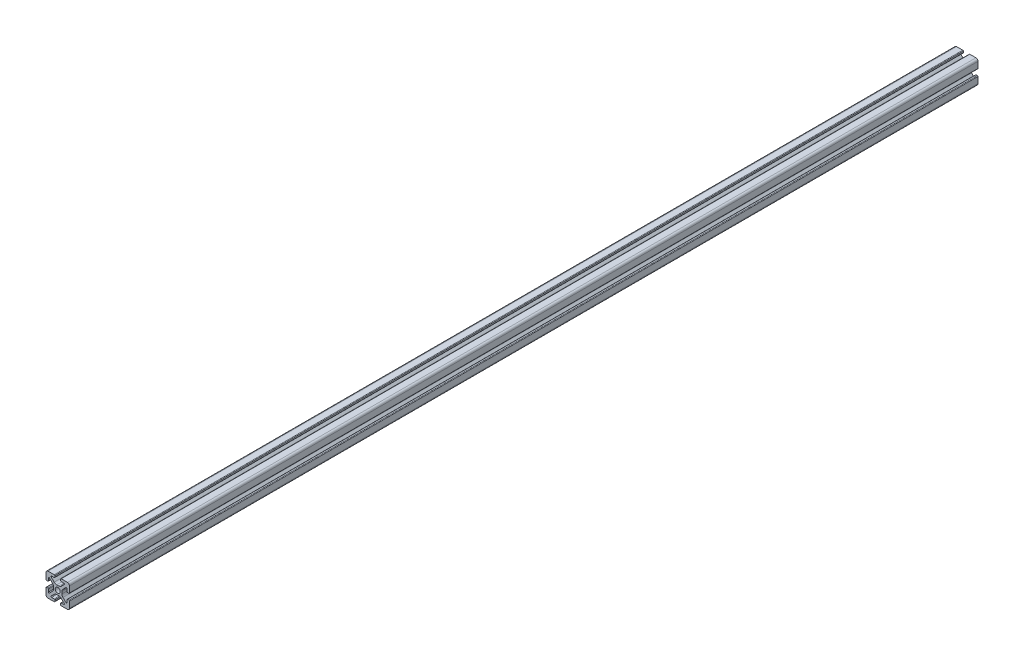
SolidWorks part; units mm, degrees
material "6061 Alloy"
ref_plane "Front Plane" through (0, 0, 0) normal (0, 0, 1) x (1, 0, 0)
ref_plane "Top Plane" through (0, 0, 0) normal (0, 1, 0) x (1, 0, 0)
ref_plane "Right Plane" through (0, 0, 0) normal (1, 0, 0) x (0, 0, -1)
sketch "Sketch2" plane through (0, 0, 0) normal (0, 0, 1) x (1, 0, 0)
  line L0 (0, 10) -> (0, -10) construction
  line L1 (-10, 0) -> (10, 0) construction
  line L2 (2.5, -10) -> (10, -10)
  line L3 (10, -10) -> (10, -2.5)
  line L4 (2.5, -10) -> (2.5, -7.9246)
  line L5 (2.5, -7.9246) -> (6.4571, -7.9246)
  line L6 (6.4571, -7.9246) -> (2.1325, -3.6)
  line L7 (0, 0) -> (10, -10) construction
  line L8 (10, -2.5) -> (7.9246, -2.5)
  line L9 (7.9246, -2.5) -> (7.9246, -6.4571)
  line L10 (7.9246, -6.4571) -> (3.6, -2.1325)
  line L11 (5.7623, -4.2948) -> (4.2948, -5.7623) construction
  circle A0 centre (0, 0) radius 2.15
  arc A1 (5.25, -7.9246) -> (5.6036, -7.0711) centre (5.25, -7.4246) ccw construction
  point P8 (0, -3.6)
  point P16 (5.0286, -5.0286)
  dimension "Center Hole Diameter" = 4.3
  dimension "D3" = 0.5
  dimension "Rail Height" = 20
  dimension "Rail Width" = 20
  dimension "T-Slot Width" = 5
  dimension "Slot Depth" = 6.4
  dimension "Slot Inner Width" = 11.5
sketch "Sketch3" plane through (0, 0, 0) normal (1, 0, 0) x (0, 0, -1)
  line L0 (-152.4, -10) -> (152.4, -10) construction
  line L1 (-127, 0) -> (127, 0) construction
  line L2 (0, 10) -> (0, -10) construction
  line L3 (0, 10) -> (0, -10) construction
  point P6 (-127, 0)
  point P8 (127, 0)
  dimension "Length" = 304.8
  dimension "D1" = 25.4
sketch "Sketch4" plane through (0, 0, 0) normal (0, 0, 1) x (1, 0, 0)
  line L0 (3, -10) -> (8.25, -10)
  line L1 (2.5, -10) -> (10, -10) construction
  line L2 (2.5, -10) -> (2.5, -7.9246) construction
  line L3 (2.5, -7.9246) -> (6.4571, -7.9246) construction
  line L4 (2.5, -8.4246) -> (2.5, -9.5)
  line L5 (3, -7.9246) -> (5.25, -7.9246)
  line L6 (0, -3.6) -> (0.8898, -3.6)
  line L7 (6.4571, -7.9246) -> (2.1325, -3.6) construction
  line L8 (3.0112, -4.4787) -> (5.6036, -7.0711)
  line L9 (10, -10) -> (10, -2.5) construction
  line L10 (7.9246, -6.4571) -> (3.6, -2.1325) construction
  line L11 (7.9246, -2.5) -> (7.9246, -6.4571) construction
  line L12 (7.9246, -5.25) -> (7.9246, -3)
  line L13 (10, -2.5) -> (7.9246, -2.5) construction
  line L14 (8.4246, -2.5) -> (9.5, -2.5)
  line L15 (10, -3) -> (10, -8.25)
  line L16 (7.0711, -5.6036) -> (4.4787, -3.0112)
  line L17 (3.6, 0) -> (3.6, -0.8898)
  line L18 (-10, 0) -> (10, 0) construction
  line L19 (0, -3.6) -> (0, -2.15)
  line L20 (0, 10) -> (0, -10) construction
  line L21 (3.6, 0) -> (2.15, 0)
  arc A0 (2.5, -9.5) -> (3, -10) centre (3, -9.5) ccw
  arc A1 (5.25, -7.9246) -> (5.6036, -7.0711) centre (5.25, -7.4246) ccw construction
  arc A2 (2.5, -8.4246) -> (3, -7.9246) centre (3, -8.4246) cw
  arc A3 (5.25, -7.9246) -> (5.6036, -7.0711) centre (5.25, -7.4246) ccw
  arc A4 (0.8898, -3.6) -> (3.0112, -4.4787) centre (0.8898, -6.6) cw
  arc A5 (8.25, -10) -> (10, -8.25) centre (8.25, -8.25) ccw
  arc A6 (7.0711, -5.6036) -> (7.9246, -5.25) centre (7.4246, -5.25) ccw
  arc A7 (7.9246, -3) -> (8.4246, -2.5) centre (8.4246, -3) cw
  arc A8 (9.5, -2.5) -> (10, -3) centre (9.5, -3) cw
  arc A9 (4.4787, -3.0112) -> (3.6, -0.8898) centre (6.6, -0.8898) cw
  circle A10 centre (0, 0) radius 2.15 construction
  arc A11 (0, -2.15) -> (2.15, 0) centre (0, 0) ccw
  dimension "D1" = 1.75
  dimension "D2" = 3
extrude "Boss-Extrude1" add sketch "Sketch4" along normal mid plane 775.4
mirror "Mirror1" about plane through (0, 0, 0) normal (1, 0, 0) of bodies 134
mirror "Mirror2" about plane through (0, 0, 0) normal (0, 1, 0) of bodies 135
equation "\"D3@Sketch2\"=\"T-Slot Width@Sketch2\"*0.1"
equation "\"D1@Sketch4\"=\"D3@Sketch2\"*3.5"
equation "\"D2@Sketch4\"=\"D3@Sketch2\"*6"
equation "\"D1@Boss-Extrude1\"=\"Length@Sketch3\""
